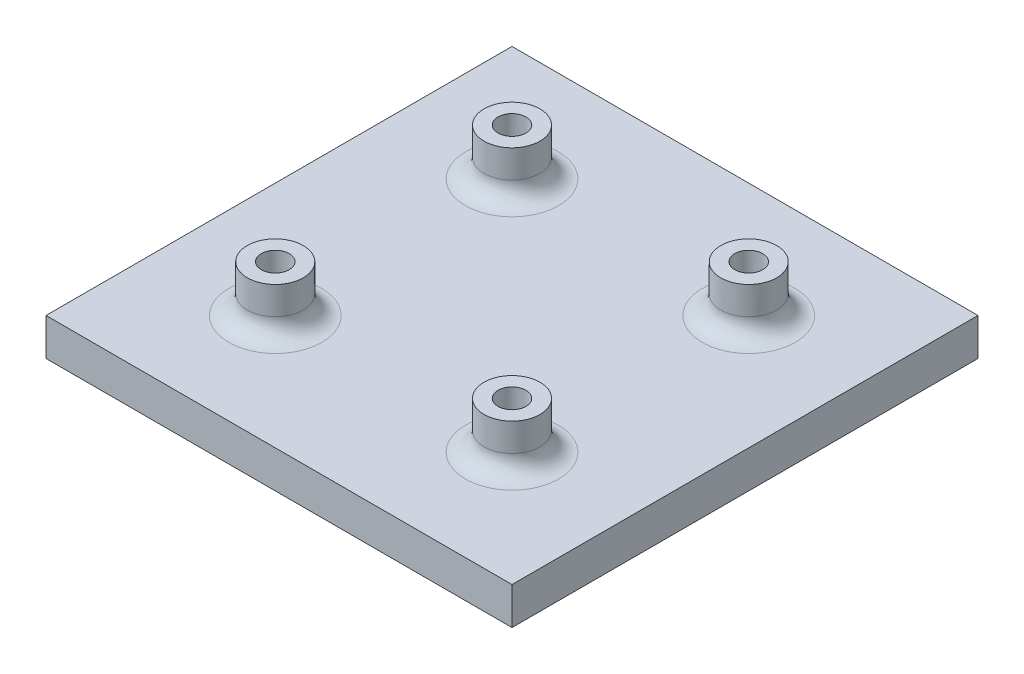
SolidWorks part; units mm, degrees
ref_plane "Front Plane" through (0, 0, 0) normal (0, 0, 1) x (1, 0, 0)
ref_plane "Top Plane" through (0, 0, 0) normal (0, 1, 0) x (1, 0, 0)
ref_plane "Right Plane" through (0, 0, 0) normal (1, 0, 0) x (0, 0, -1)
sketch "Sketch2" plane through (0, 0, 0) normal (0, 1, 0) x (1, 0, 0)
  line L1 (0, 0) -> (50, 0)
  line L2 (0, 0) -> (0, 50)
  line L3 (0, 50) -> (50, 50)
  line L4 (50, 0) -> (50, 50)
  dimension "D1" = 50
extrude "Boss-Extrude1" add sketch "Sketch2" along normal blind 4
sketch "Sketch3" plane through (0, 4, 0) normal (0, 1, 0) x (1, 0, 0)
  line L0 (0, 50) -> (50, 0) construction
  line L1 (0, 0) -> (50, 50) construction
  circle A0 centre (12.3, 37.7) radius 1.5
  circle A1 centre (12.3, 12.3) radius 1.5
  circle A2 centre (37.7, 37.7) radius 1.5
  circle A3 centre (37.7, 12.3) radius 1.5
  dimension "D1" = 3
  dimension "D3" = 25.4
  dimension "D4" = 0
  dimension "D5" = 25.4
  dimension "D2" = 25.4
extrude "Cut-Extrude1" cut sketch "Sketch3" against normal blind 4
sketch "Sketch4" plane through (0, 4, 0) normal (0, 1, 0) x (1, 0, 0)
  circle A0 centre (12.3, 37.7) radius 1.5
  circle A1 centre (12.3, 37.7) radius 3
  dimension "D1" = 6
extrude "Boss-Extrude2" add sketch "Sketch4" along normal blind 5
ref_plane "Plane1" through (25, 0, 0) normal (-1, 0, 0) x (0, 0, 1)
ref_plane "Plane2" through (0, 0, -25) normal (0, 0, 1) x (1, 0, 0)
mirror "Mirror1" about plane through (0, 0, -25) normal (0, 0, 1) of "Boss-Extrude2"
mirror "Mirror2" about plane through (25, 0, 0) normal (-1, 0, 0) of "Mirror1", "Boss-Extrude2"
fillet "Fillet1" radius 2 4 edges at (37.7, 4, -15.3) (37.7, 4, -34.7) (12.3, 4, -40.7) (12.3, 4, -15.3)
sketch "Sketch6" plane through (0, 0, 0) normal (0, -1, 0) x (1, 0, 0)
  line L4 (0, 0) -> (0, -50)
  line L5 (0, -50) -> (50, -50)
  line L6 (50, -50) -> (50, 0)
  line L7 (50, 0) -> (0, 0)
  line L8 (0, 0) -> (0, -50)
  line L9 (0, -50) -> (50, -50)
  line L10 (50, -50) -> (50, 0)
  line L11 (50, 0) -> (0, 0)
  dimension "D1" = 0
extrude "Boss-Extrude3" add sketch "Sketch6" against normal blind 4
